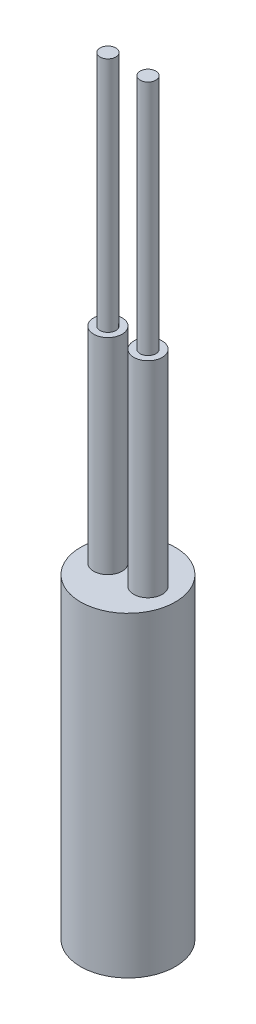
SolidWorks part; units mm, degrees
ref_plane "Front Plane" through (0, 0, 0) normal (0, 0, 1) x (1, 0, 0)
ref_plane "Top Plane" through (0, 0, 0) normal (0, 1, 0) x (1, 0, 0)
ref_plane "Right Plane" through (0, 0, 0) normal (1, 0, 0) x (0, 0, -1)
sketch "Sketch1" plane through (0, 0, 0) normal (0, 1, 0) x (1, 0, 0)
  circle A0 centre (0, 0) radius 3
  dimension "D1" = 6
extrude "Boss-Extrude1" add sketch "Sketch1" along normal blind 20
sketch "Sketch2" plane through (0, 20, 0) normal (0, 1, 0) x (1, 0, 0)
  line L0 (0, -3) -> (0, 3) construction
  circle A0 centre (1.27, 0) radius 0.9
  circle A1 centre (0, 0) radius 3 construction
  circle A2 centre (-1.27, 0) radius 0.9
  dimension "D1" = 1.8
  dimension "D2" = 2.54
extrude "Boss-Extrude2" add sketch "Sketch2" along normal blind 13
sketch "Sketch3" plane through (0, 33, 0) normal (0, 1, 0) x (1, 0, 0)
  circle A0 centre (1.27, 0) radius 0.5
  circle A1 centre (-1.27, 0) radius 0.5
  dimension "D1" = 1
extrude "Boss-Extrude3" add sketch "Sketch3" along normal blind 15
